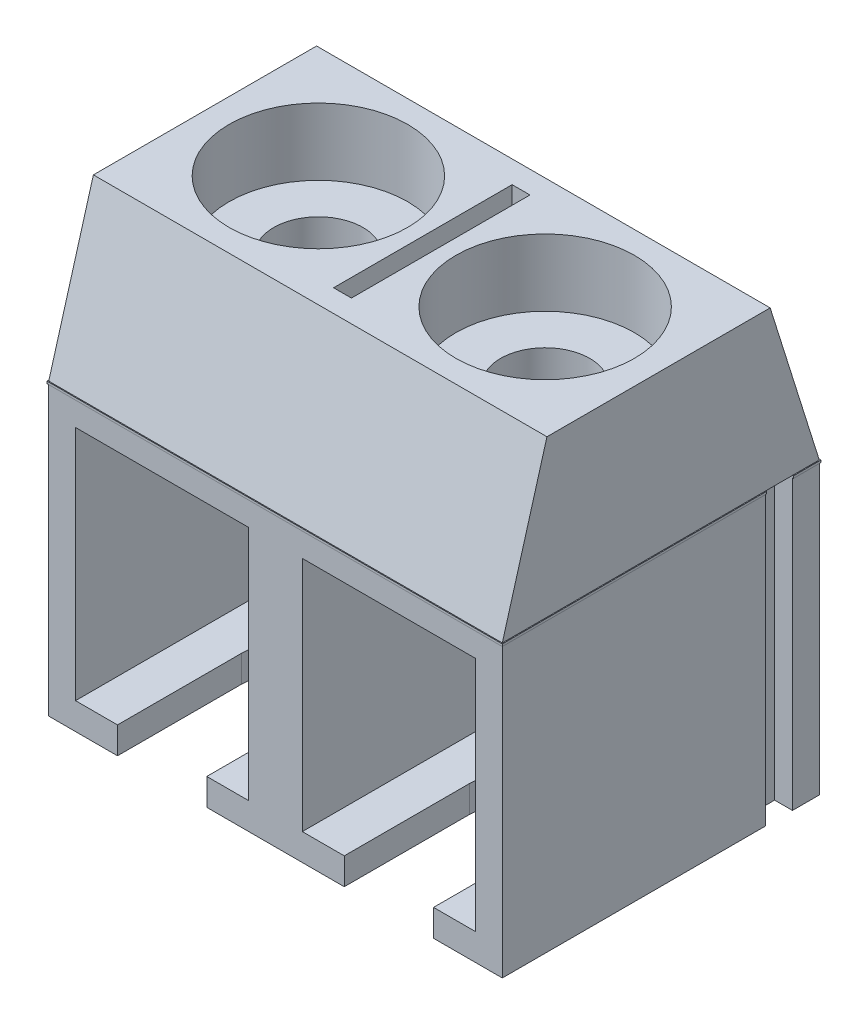
SolidWorks part; units mm, degrees
material "ABS"
ref_plane "Front Plane" through (0, 0, 0) normal (0, 0, 1) x (1, 0, 0)
ref_plane "Top Plane" through (0, 0, 0) normal (0, 1, 0) x (1, 0, 0)
ref_plane "Right Plane" through (0, 0, 0) normal (1, 0, 0) x (0, 0, -1)
sketch "Sketch1" plane through (0, 0, 0) normal (0, 1, 0) x (1, 0, 0)
  line L1 (0, 0) -> (-10.16, 0)
  line L2 (0, 0) -> (0, -7.1)
  line L3 (0, -7.1) -> (-10.16, -7.1)
  line L4 (-10.16, 0) -> (-10.16, -7.1)
  dimension "D1" = 10.16
  dimension "D2" = 7.1
extrude "Boss-Extrude1" add sketch "Sketch1" along normal blind 6.5
ref_plane "Plane1" through (0, 6.5, 0) normal (0, 1, 0) x (1, 0, 0)
sketch "Sketch3" plane through (0, 6.5, 0) normal (0, 1, 0) x (1, 0, 0)
  line L1 (-10.16, 0) -> (0, 0)
  line L2 (-10.16, 0) -> (-10.16, -7.1)
  line L3 (-10.16, -7.1) -> (0, -7.1)
  line L4 (0, 0) -> (0, -7.1)
ref_plane "Plane2" through (0, 10, 0) normal (0, 1, 0) x (1, 0, 0)
sketch "Sketch4" plane through (0, 10, 0) normal (0, 1, 0) x (1, 0, 0)
  line L0 (-10.16, 0) -> (-10.16, -7.1) construction
  line L1 (-10.16, -1.1) -> (0, -1.1)
  line L2 (-10.16, -1.1) -> (-10.16, -6.1)
  line L3 (-10.16, -6.1) -> (0, -6.1)
  line L4 (0, -1.1) -> (0, -6.1)
  line L5 (0, 0) -> (0, -7.1) construction
  line L6 (-10.16, -7.1) -> (0, -7.1) construction
  dimension "D1" = 5
  dimension "D2" = 1
loft "Loft1" add profiles "Sketch4" section "Sketch4" section face at (-5.08, 6.5, 3.55)
sketch "Sketch5" plane through (0, 0, 7.1) normal (0, 0, 1) x (1, 0, 0)
  line L5 (-5.68, 5.9) -> (-4.48, 5.9)
  line L6 (-5.68, 5.9) -> (-5.68, 0.6)
  line L7 (-5.68, 0.6) -> (-4.48, 0.6)
  line L8 (-9.56, 0.6) -> (-0.6, 0.6)
  line L9 (-0.6, 0.6) -> (-0.6, 5.9)
  line L10 (-0.6, 5.9) -> (-9.56, 5.9)
  line L11 (-9.56, 5.9) -> (-9.56, 0.6)
  line L12 (-9.56, 0.6) -> (-0.6, 0.6)
  line L13 (-0.6, 0.6) -> (-0.6, 5.9)
  line L14 (-0.6, 5.9) -> (-9.56, 5.9)
  line L15 (-9.56, 5.9) -> (-9.56, 0.6)
  line L16 (-4.48, 5.9) -> (-4.48, 0.6)
  point P4 (-5.08, 5.9)
  point P5 (-5.08, 5.9)
  dimension "D2" = 1.2
  dimension "D1" = 0.6
extrude "Cut-Extrude1" cut sketch "Sketch5" against normal offset from surface (6.6 mm away) 0.5 contours L14 L15 L12 L6 | L14 L16 L12 L13 up to face at (-5.08, 3.25, 0)
sketch "Sketch6" plane through (0, 10, 0) normal (0, 1, 0) x (1, 0, 0)
  line L1 (0, -6.1) -> (0, -1.1) construction
  line L14 (-5.28, -1.6) -> (-4.88, -1.6)
  line L15 (-5.28, -1.6) -> (-5.28, -5.6)
  line L16 (-5.28, -5.6) -> (-4.88, -5.6)
  line L17 (-4.88, -1.6) -> (-4.88, -5.6)
  line L19 (0, -1.1) -> (-10.16, -1.1) construction
  line L20 (-10.16, -6.1) -> (0, -6.1) construction
  line L21 (-5.08, -1.1) -> (-10.16, -1.1) construction
  line L22 (-5.08, -1.1) -> (0, -1.1) construction
  line L23 (-10.16, -1.1) -> (-10.16, -6.1) construction
  circle A0 centre (-7.62, -3.6) radius 2
  circle A1 centre (-2.54, -3.6) radius 2
  point P11 (0, -3.6)
  point P25 (-7.62, -1.1)
  point P28 (-10.16, -3.6)
  dimension "D1" = 4
  dimension "D2" = 4
  dimension "D6" = 0.4
  dimension "D3" = 0.5
  dimension "D4" = 0.5
  dimension "D5" = 5.08
  dimension "D7" = 0.2
extrude "Cut-Extrude2" cut sketch "Sketch6" against normal blind 1.5
sketch "Sketch7" plane through (0, 8.5, 0) normal (0, 1, 0) x (1, 0, 0)
  circle A0 centre (-7.62, -3.6) radius 1
  circle A1 centre (-2.54, -3.6) radius 1
  dimension "D1" = 2
  dimension "D2" = 2
extrude "Cut-Extrude3" cut sketch "Sketch7" against normal up to next
sketch "Sketch8" plane through (0, 0, 0) normal (1, 0, 0) x (0, 0, -1)
  line L0 (-7.1, 0) -> (0, 0) construction
  line L1 (-0.6, 0) -> (-1.2, 0)
  line L2 (-0.6, 0) -> (-0.6, 6.5)
  line L3 (-0.6, 6.5) -> (-1.2, 6.5)
  line L4 (-1.2, 0) -> (-1.2, 6.5)
  line L5 (0, 6.5) -> (0, 0) construction
  dimension "D1" = 0.6
  dimension "D2" = 0
  dimension "D3" = 0.6
extrude "Cut-Extrude4" cut sketch "Sketch8" against normal blind 0.4
sketch "Sketch9" plane through (-10.16, 0, 0) normal (-1, 0, 0) x (0, 0, 1)
  line L0 (0, 0) -> (7.1, 0) construction
  line L1 (0.6, 0) -> (1.2, 0)
  line L2 (0.6, 0) -> (0.6, 6.5)
  line L3 (0.6, 6.5) -> (1.2, 6.5)
  line L4 (1.2, 0) -> (1.2, 6.5)
  line L5 (0, 6.5) -> (0, 0) construction
  dimension "D1" = 0.6
  dimension "D2" = 0.6
  dimension "D3" = 0
extrude "Boss-Extrude2" add sketch "Sketch9" along normal blind 0.4
sketch "Sketch10" plane through (-10.16, 0, 0) normal (-1, 0, 0) x (0, 0, 1)
  line L0 (7.1, 6.5) -> (7.1, 0) construction
  line L1 (0, 6.5) -> (7.1, 6.5)
  line L2 (0, 6.5) -> (0, 6.45)
  line L3 (0, 6.45) -> (7.1, 6.45)
  line L4 (7.1, 6.5) -> (7.1, 6.45)
  dimension "D1" = 0.05
extrude "Boss-Extrude3" add sketch "Sketch10" along normal blind 0.02
sketch "Sketch11" plane through (0, 0, 7.1) normal (0, 0, 1) x (1, 0, 0)
  line L0 (0, 10) -> (0, 6.5) construction
  line L1 (-10.18, 6.45) -> (0.02, 6.45)
  line L2 (-10.18, 6.45) -> (-10.18, 6.5)
  line L3 (-10.18, 6.5) -> (0.02, 6.5)
  line L4 (0.02, 6.45) -> (0.02, 6.5)
  dimension "D1" = 0.05
  dimension "D2" = 0.02
extrude "Boss-Extrude4" add sketch "Sketch11" along normal blind 0.02
sketch "Sketch13" plane through (0, 0, 7.1) normal (0, 0, -1) x (-1, 0, 0)
  line L1 (-0.02, 6.5) -> (0, 6.5)
  line L2 (-0.02, 6.5) -> (-0.02, 6.45)
  line L3 (-0.02, 6.45) -> (0, 6.45)
  line L4 (0, 6.5) -> (0, 6.45)
extrude "Boss-Extrude8" add sketch "Sketch13" along normal up to surface (5.9 mm away) up to face at (-0.2, 3.25, 1.2)
sketch "Sketch14" plane through (0, 0, 0) normal (0, 0, -1) x (-1, 0, 0)
  line L1 (10.18, 6.5) -> (10.16, 6.5)
  line L2 (10.18, 6.5) -> (10.18, 6.45)
  line L3 (10.18, 6.45) -> (10.16, 6.45)
  line L4 (10.16, 6.5) -> (10.16, 6.45)
extrude "Boss-Extrude9" add sketch "Sketch14" along normal blind 0.02
sketch "Sketch15" plane through (-10.16, 0, 0) normal (1, 0, 0) x (0, 0, -1)
  line L1 (0, 6.5) -> (0.02, 6.5)
  line L2 (0, 6.5) -> (0, 6.45)
  line L3 (0, 6.45) -> (0.02, 6.45)
  line L4 (0.02, 6.5) -> (0.02, 6.45)
extrude "Boss-Extrude10" add sketch "Sketch15" along normal offset from surface (10.18 mm away) 0.02 up to face at (0, 3.225, 4.15) offset beyond the face yes
sketch "Sketch16" plane through (0, 0, 0) normal (0, 0, 1) x (1, 0, 0)
  line L1 (0, 6.5) -> (0.02, 6.5)
  line L2 (0, 6.5) -> (0, 6.45)
  line L3 (0, 6.45) -> (0.02, 6.45)
  line L4 (0.02, 6.5) -> (0.02, 6.45)
extrude "Boss-Extrude11" add sketch "Sketch16" along normal up to surface (0.6 mm away) up to face at (-0.2, 3.25, 0.6)
sketch "Sketch18" plane through (0, 0, 0) normal (0, -1, 0) x (1, 0, 0)
  line L0 (-7.62, 4.32) -> (-7.62, 7.92) construction
  line L1 (-8.62, 4.32) -> (-8.62, 7.92)
  line L2 (-6.62, 4.32) -> (-6.62, 7.92)
  line L3 (-2.54, 4.3) -> (-2.54, 7.9) construction
  line L4 (-3.54, 4.3) -> (-3.54, 7.9)
  line L5 (-1.54, 4.3) -> (-1.54, 7.9)
  line L7 (-10.16, 7.1) -> (0, 7.1) construction
  line L8 (-10.18, 7.12) -> (0.02, 7.12) construction
  arc A0 (-8.62, 4.32) -> (-6.62, 4.32) centre (-7.62, 4.32) ccw
  arc A1 (-6.62, 7.92) -> (-8.62, 7.92) centre (-7.62, 7.92) ccw
  arc A2 (-3.54, 4.3) -> (-1.54, 4.3) centre (-2.54, 4.3) ccw
  arc A3 (-1.54, 7.9) -> (-3.54, 7.9) centre (-2.54, 7.9) ccw
  point P3 (-7.62, 6.12)
  point P8 (-2.54, 6.1)
  dimension "D3" = 3.6
  dimension "D4" = 3.6
  dimension "D1" = 2
  dimension "D2" = 2
  dimension "D5" = 2.8
  dimension "D6" = 2.8
extrude "Cut-Extrude5" cut sketch "Sketch18" against normal up to next
